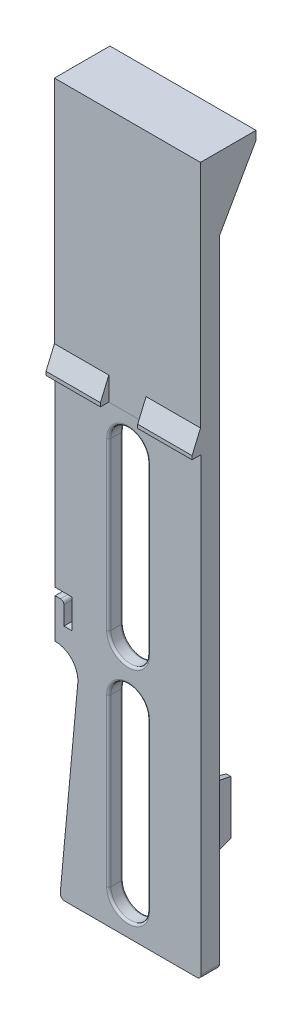
SolidWorks part; units mm, degrees
ref_plane "Front Plane" through (0, 0, 0) normal (0, 0, 1) x (1, 0, 0)
ref_plane "Top Plane" through (0, 0, 0) normal (0, 1, 0) x (1, 0, 0)
ref_plane "Right Plane" through (0, 0, 0) normal (1, 0, 0) x (0, 0, -1)
sketch "Sketch1" plane through (0, 0, 0) normal (0, 0, 1) x (1, 0, 0)
  line L0 (0, 0) -> (0, 100.3393) construction
  line L2 (-12.7, 123.19) -> (12.7, 123.19)
  line L3 (-12.7, 123.19) -> (-12.7, 0)
  line L4 (-12.7, 0) -> (12.7, 0)
  line L5 (12.7, 123.19) -> (12.7, 0)
  line L6 (-12.7, 123.19) -> (12.7, 0) construction
  line L7 (-12.7, 0) -> (12.7, 123.19) construction
  point P3 (0, 61.595)
  dimension "D1" = 25.4
  dimension "D2" = 123.19
extrude "Boss-Extrude1" add sketch "Sketch1" against normal blind 2.032
sketch "Sketch2" plane through (0, 0, -2.032) normal (0, 0, -1) x (-1, 0, 0)
  line L4 (-12.7, 123.19) -> (-12.7, 0)
  line L5 (-12.7, 0) -> (12.7, 0)
  line L6 (12.7, 0) -> (12.7, 123.19)
  line L7 (12.7, 123.19) -> (-12.7, 123.19)
  line L8 (-12.7, 123.19) -> (-12.7, 0)
  line L9 (-12.7, 0) -> (12.7, 0)
  line L10 (12.7, 0) -> (12.7, 123.19)
  line L11 (12.7, 123.19) -> (-12.7, 123.19)
  dimension "D1" = 0
extrude "Extrude-Thin1" add sketch "Sketch2" along normal offset from surface (1.143 mm away) 3.175 thin up to face at (0, 61.595, 0) thin type one direction reverse wall 1.524
sketch "Sketch3" plane through (0, 0, 0) normal (0, 0, 1) x (1, 0, 0)
  line L0 (0, 123.19) -> (0, 0) construction
  line L1 (12.7, 123.19) -> (-12.7, 123.19) construction
  line L2 (0, 34.7345) -> (0, 5.8293) construction
  line L3 (3.3655, 34.7345) -> (3.3655, 5.8293)
  line L4 (-3.3655, 34.7345) -> (-3.3655, 5.8293)
  line L5 (-12.7, 0) -> (12.7, 0) construction
  arc A0 (3.3655, 34.7345) -> (-3.3655, 34.7345) centre (0, 34.7345) ccw
  arc A1 (-3.3655, 5.8293) -> (3.3655, 5.8293) centre (0, 5.8293) ccw
  point P7 (0, 20.2819)
  dimension "D3" = 2.4638
  dimension "D1" = 6.731
  dimension "D2" = 35.6362
extrude "Cut-Extrude1" cut sketch "Sketch3" against normal through all
pattern_linear "LPattern1" count 2 spacing 38.608 along (0, 1, 0) of "Cut-Extrude1"
sketch "Sketch4" plane through (0, 0, 0) normal (0, 0, 1) x (1, 0, 0)
  line L0 (-11.8872, 0) -> (-8.763, 33.9877)
  line L1 (-12.7, 0) -> (12.7, 0) construction
  line L2 (-12.7, 38.3032) -> (-22.3348, 38.3032) construction
  line L3 (-12.7, 123.19) -> (-12.7, 0) construction
  line L4 (12.7, 0) -> (12.7, 123.19) construction
  arc A0 (-8.763, 33.9877) -> (-12.7, 38.3032) centre (-12.7, 34.3496) ccw
  dimension "D1" = 24.5872
  dimension "D2" = 38.3032
  dimension "D3" = 21.463
extrude "Cut-Extrude2" cut sketch "Sketch4" against normal through all and the other way through all
sketch "Sketch5" plane through (0, 0, 0) normal (0, 0, 1) x (1, 0, 0)
  line L0 (-12.7, 46.4312) -> (-9.7282, 46.4312)
  line L1 (-12.7, 123.19) -> (-12.7, 38.3032) construction
  line L2 (-9.7282, 46.4312) -> (-9.7282, 41.3512)
  line L3 (-9.7282, 41.3512) -> (-11.176, 41.3512)
  line L4 (-11.176, 41.3512) -> (-11.176, 45.1612)
  line L5 (-11.176, 45.1612) -> (-12.7, 45.1612)
  line L6 (-12.7, 45.1612) -> (-12.7, 46.4312)
  line L7 (-11.8872, 0) -> (12.7, 0) construction
  dimension "D1" = 1.27
  dimension "D2" = 1.4478
  dimension "D3" = 5.08
  dimension "D4" = 1.524
  dimension "D5" = 45.1612
extrude "Cut-Extrude3" cut sketch "Sketch5" against normal through all
sketch "Sketch6" plane through (0, 0, -2.032) normal (0, 0, -1) x (-1, 0, 0)
  line L0 (0, 0) -> (0, 133.807) construction
  line L1 (0, 6.0808) -> (0, 72.6186) construction
  line L2 (-7.1374, 6.0808) -> (-7.1374, 72.6186)
  line L3 (7.1374, 6.0808) -> (7.1374, 72.6186)
  line L4 (11.8872, 0) -> (-12.7, 0) construction
  line L5 (-8.7884, 6.0808) -> (-8.7884, 72.6186)
  line L6 (8.7884, 6.0808) -> (8.7884, 72.6186)
  arc A0 (-7.1374, 6.0808) -> (7.1374, 6.0808) centre (0, 6.0808) ccw
  arc A1 (7.1374, 72.6186) -> (-7.1374, 72.6186) centre (0, 72.6186) ccw
  arc A2 (8.7884, 72.6186) -> (-8.7884, 72.6186) centre (0, 72.6186) ccw
  arc A3 (-8.7884, 6.0808) -> (8.7884, 6.0808) centre (0, 6.0808) ccw
  point P5 (0, 39.3497)
  dimension "D3" = 79.756
  dimension "D1" = 14.2748
  dimension "D2" = 80.8126
  dimension "D4" = 1.651
extrude "Boss-Extrude2" add sketch "Sketch6" along normal up to surface (1.143 mm away) up to face at (-3.1127, 53.9418, -3.175)
sketch "Sketch7" plane through (0, 0, -3.175) normal (0, 0, -1) x (-1, 0, 0)
  line L1 (-6.3451, 0) -> (7.3026, 0)
  line L2 (-6.3451, 0) -> (-6.3451, -4.1989)
  line L3 (-6.3451, -4.1989) -> (7.3026, -4.1989)
  line L4 (7.3026, 0) -> (7.3026, -4.1989)
extrude "Cut-Extrude4" cut sketch "Sketch7" against normal through all
sketch "Sketch8" plane through (0, 0, -3.175) normal (0, 0, -1) x (-1, 0, 0)
  circle A0 centre (0, 6.0808) radius 7.1374
extrude "Cut-Extrude5" cut sketch "Sketch8" against normal up to surface (1.143 mm away) up to face at (0, 27.8828, -2.032)
fillet "Fillet1" radius 0.254 2 edges at (-3.7372, 0, -2.6035) (3.7372, 0, -2.6035)
sketch "Sketch9" plane through (0, 0, -2.032) normal (0, 0, -1) x (-1, 0, 0)
  line L0 (3.3655, 34.7345) -> (3.3655, 5.8293) construction
  line L1 (-3.3655, 5.8293) -> (-3.3655, 34.7345) construction
  line L2 (-3.3655, 44.4373) -> (-3.3655, 73.3425) construction
  line L3 (-7.1374, 72.6186) -> (-7.1374, 6.0808)
  line L4 (-4.5477, 0) -> (4.5477, 0)
  line L5 (7.1374, 6.0808) -> (7.1374, 72.6186)
  line L6 (-7.1374, 72.6186) -> (-7.1374, 6.0808)
  line L7 (-4.5477, 0) -> (4.5477, 0)
  line L8 (7.1374, 6.0808) -> (7.1374, 72.6186)
  line L9 (3.3655, 73.3425) -> (3.3655, 44.4373) construction
  line L10 (3.3655, 34.7345) -> (3.3655, 5.8293)
  line L11 (-3.3655, 5.8293) -> (-3.3655, 34.7345)
  line L12 (-3.3655, 44.4373) -> (-3.3655, 73.3425)
  line L13 (3.3655, 73.3425) -> (3.3655, 44.4373)
  arc A0 (-3.3655, 5.8293) -> (3.3655, 5.8293) centre (0, 5.8293) ccw construction
  arc A1 (-3.3655, 5.8293) -> (3.3655, 5.8293) centre (0, 5.8293) ccw
  arc A2 (3.3655, 34.7345) -> (-3.3655, 34.7345) centre (0, 34.7345) ccw construction
  arc A3 (-3.3655, 44.4373) -> (3.3655, 44.4373) centre (0, 44.4373) ccw construction
  arc A4 (3.3655, 34.7345) -> (-3.3655, 34.7345) centre (0, 34.7345) ccw
  arc A5 (-7.1374, 6.0808) -> (-4.3914, 0.4542) centre (0, 6.0808) ccw
  arc A6 (-4.5477, 0) -> (-4.3914, 0.4542) centre (-4.5477, 0.254) ccw
  arc A7 (4.3914, 0.4542) -> (4.5477, 0) centre (4.5477, 0.254) ccw
  arc A8 (4.3914, 0.4542) -> (7.1374, 6.0808) centre (0, 6.0808) ccw
  arc A9 (7.1374, 72.6186) -> (-7.1374, 72.6186) centre (0, 72.6186) ccw
  arc A10 (-7.1374, 6.0808) -> (-4.3914, 0.4542) centre (0, 6.0808) ccw
  arc A11 (-4.5477, 0) -> (-4.3914, 0.4542) centre (-4.5477, 0.254) ccw
  arc A12 (4.3914, 0.4542) -> (4.5477, 0) centre (4.5477, 0.254) ccw
  arc A13 (4.3914, 0.4542) -> (7.1374, 6.0808) centre (0, 6.0808) ccw
  arc A14 (7.1374, 72.6186) -> (-7.1374, 72.6186) centre (0, 72.6186) ccw
  arc A15 (-3.3655, 44.4373) -> (3.3655, 44.4373) centre (0, 44.4373) ccw
  arc A16 (3.3655, 73.3425) -> (-3.3655, 73.3425) centre (0, 73.3425) ccw construction
  arc A17 (3.3655, 73.3425) -> (-3.3655, 73.3425) centre (0, 73.3425) ccw
  dimension "D1" = 0
extrude "Boss-Extrude3" add sketch "Sketch9" along normal blind 0.508
sketch "Sketch10" plane through (0, 0, -2.032) normal (0, 0, -1) x (-1, 0, 0)
  line L0 (8.7884, 34.9243) -> (8.7884, 72.6186) construction
  line L1 (11.176, 37.9977) -> (11.176, 41.3512) construction
  line L2 (11.176, 41.3512) -> (9.7282, 41.3512) construction
  line L3 (9.7282, 41.3512) -> (9.7282, 46.4312) construction
  line L4 (9.7282, 46.4312) -> (11.176, 46.4312) construction
  line L5 (8.7884, 34.9243) -> (8.7884, 48.0822)
  line L6 (11.176, 37.9977) -> (11.176, 41.3512)
  line L7 (11.176, 41.3512) -> (9.7282, 41.3512)
  line L8 (9.7282, 41.3512) -> (9.7282, 46.4312)
  line L9 (9.7282, 46.4312) -> (11.176, 46.4312)
  line L10 (11.176, 46.4312) -> (11.176, 121.666) construction
  line L11 (11.176, 46.4312) -> (11.176, 48.0822)
  line L12 (11.176, 48.0822) -> (8.7884, 48.0822)
  arc A0 (11.176, 37.9977) -> (8.7884, 34.9243) centre (12.7, 34.3496) ccw construction
  arc A1 (11.176, 37.9977) -> (8.7884, 34.9243) centre (12.7, 34.3496) ccw
  dimension "D1" = 1.651
extrude "Boss-Extrude4" add sketch "Sketch10" along normal up to surface (1.143 mm away) up to face at (-11.9342, 41.6747, -3.175)
sketch "Sketch11" plane through (0, 0, -2.032) normal (0, 0, -1) x (-1, 0, 0)
  line L0 (8.7884, 72.6186) -> (8.7884, 121.666)
  line L1 (-8.7884, 72.6186) -> (-8.7884, 121.666)
  line L2 (11.176, 121.666) -> (-11.176, 121.666) construction
  line L3 (8.7884, 121.666) -> (7.1374, 121.666)
  line L4 (0, 0) -> (0, 145.7514) construction
  line L5 (-7.1374, 72.6186) -> (-7.1374, 121.666)
  line L7 (7.1374, 72.6186) -> (7.1374, 121.666)
  line L8 (-8.7884, 72.6186) -> (-7.1374, 72.6186)
  line L9 (7.1374, 72.6186) -> (8.7884, 72.6186)
  line L10 (-7.1374, 121.666) -> (-8.7884, 121.666)
  dimension "D1" = 1.651
  dimension "D2" = 1.651
extrude "Boss-Extrude5" add sketch "Sketch11" along normal up to surface (1.143 mm away)
sketch "Sketch12" plane through (0, 0, -2.032) normal (0, 0, -1) x (-1, 0, 0)
  line L0 (0, 0) -> (0, 135.5833) construction
  line L1 (0, 121.666) -> (0, 80.5241)
  line L2 (7.1374, 121.666) -> (-7.1374, 121.666) construction
  arc A1 (7.1374, 77.7463) -> (-7.1374, 77.7463) centre (0, 72.6186) ccw construction
  dimension "D1" = 7.9055
extrude "Extrude-Thin4" add sketch "Sketch12" along normal up to surface (1.143 mm away) thin thin type mid plane wall 1.651
sketch "Sketch13" plane through (0, 0, -2.032) normal (0, 0, -1) x (-1, 0, 0)
  line L0 (9.9822, 48.0822) -> (9.9822, 56.894) construction
  line L1 (11.176, 48.0822) -> (8.7884, 48.0822) construction
  line L2 (9.9822, 50.8308) -> (-19.4969, 49.4381) construction
  circle A0 centre (9.9822, 50.8308) radius 1.3927
  circle A1 centre (-10.0834, 49.8828) radius 1.4426
extrude "Boss-Extrude6" add sketch "Sketch13" along normal up to surface (1.143 mm away)
sketch "Sketch14" plane through (0, 0, -2.032) normal (0, 0, -1) x (-1, 0, 0)
  line L4 (7.5148, 1.524) -> (11.176, 1.524)
  line L5 (11.176, 1.524) -> (11.176, 7.737)
  line L6 (11.176, 7.737) -> (8.7884, 33.7114)
  line L7 (8.7884, 33.7114) -> (8.7884, 6.0808)
  line L8 (7.5148, 1.524) -> (11.176, 1.524)
  line L9 (11.176, 1.524) -> (11.176, 7.737)
  line L10 (11.176, 7.737) -> (8.7884, 33.7114)
  line L11 (8.7884, 33.7114) -> (8.7884, 6.0808)
  arc A1 (7.5148, 1.524) -> (8.7884, 6.0808) centre (0, 6.0808) ccw
  arc A2 (7.5148, 1.524) -> (8.7884, 6.0808) centre (0, 6.0808) ccw
  dimension "D1" = 0
extrude "Boss-Extrude7" add sketch "Sketch14" along normal up to surface (1.143 mm away)
fillet "Fillet2" radius 0.381 16 edges at (0, 76.708, 0) (3.3655, 58.8899, 0) (0, 41.0718, 0) (0, 38.1, 0) (3.3655, 20.2819, 0) (0, 2.4638, 0) (0, 38.1, -2.54) (-3.3655, 20.2819, -2.54) (0, 2.4638, -2.54) (0, 76.708, -2.54) (-3.3655, 58.8899, -2.54) (0, 41.0718, -2.54) (-3.3655, 58.8899, 0) (-3.3655, 20.2819, 0) (3.3655, 20.2819, -2.54) (3.3655, 58.8899, -2.54)
sketch "Sketch15" plane through (0, 0, 0) normal (0, 0, 1) x (1, 0, 0)
  line L0 (-12.7, 123.19) -> (-12.7, 46.4312) construction
  line L1 (12.7, 123.19) -> (-12.7, 123.19) construction
  line L2 (12.7, 0) -> (12.7, 123.19) construction
  line L3 (-12.7, 123.19) -> (-12.7, 79.121)
  line L4 (12.7, 123.19) -> (-12.7, 123.19)
  line L5 (12.7, 79.121) -> (12.7, 123.19)
  line L6 (-12.7, 79.121) -> (12.7, 79.121)
  dimension "D1" = 44.069
extrude "Boss-Extrude8" add sketch "Sketch15" along normal blind 0.127
sketch "Sketch16" plane through (0, 0, 0) normal (1, 0, 0) x (0, 0, -1)
  line L0 (-0.127, 79.121) -> (-1.5875, 79.121)
  line L1 (-1.5875, 79.121) -> (-1.5875, 79.756)
  line L2 (-1.5875, 79.756) -> (-0.127, 83.185)
  line L3 (-0.127, 79.121) -> (-0.127, 123.19) construction
  line L4 (-0.127, 83.185) -> (-0.127, 79.121)
  line L5 (0, 0) -> (0, 79.121) construction
  dimension "D1" = 1.5875
  dimension "D2" = 0.635
  dimension "D3" = 4.064
extrude "Boss-Extrude9" add sketch "Sketch16" along normal up to surface and the other way up to surface up to face at (12.7, 67.437, -1.016) other way up to face at (-12.7, 41.7322, -1.5875)
sketch "Sketch17" plane through (0, 123.19, 0) normal (0, 1, 0) x (1, 0, 0)
  line L0 (0, -0.127) -> (0, -13.26) construction
  line L1 (12.7, -0.127) -> (-12.7, -0.127) construction
  line L3 (-3.2385, -6.3417) -> (3.2385, -6.3417)
  line L4 (-3.2385, -6.3417) -> (-3.2385, -0.127)
  line L5 (-3.2385, -0.127) -> (3.2385, -0.127)
  line L6 (3.2385, -6.3417) -> (3.2385, -0.127)
  line L7 (-3.2385, -6.3417) -> (3.2385, -0.127) construction
  line L8 (-3.2385, -0.127) -> (3.2385, -6.3417) construction
  point P5 (0, -3.2343)
  dimension "D1" = 6.477
extrude "Cut-Extrude6" cut sketch "Sketch17" against normal through all
fillet "Fillet3" radius 0.5842 1 edges at (-11.176, 45.1612, -1.5875)
sketch "Sketch18" plane through (0, 0, -3.175) normal (0, 0, -1) x (-1, 0, 0)
  line L0 (-7.1374, 6.0808) -> (-7.1374, 72.6186) construction
  line L1 (-7.1374, 25.4) -> (-8.7884, 25.4)
  line L2 (-7.1374, 25.4) -> (-7.1374, 12.7)
  line L3 (-7.1374, 12.7) -> (-8.7884, 12.7)
  line L4 (-8.7884, 25.4) -> (-8.7884, 12.7)
  line L5 (-8.7884, 6.0808) -> (-8.7884, 49.2472) construction
  line L6 (-4.5477, 0) -> (-12.7, 0) construction
  dimension "D1" = 12.7
  dimension "D2" = 12.7
extrude "Boss-Extrude11" add sketch "Sketch18" along normal blind 6.35 draft 4
sketch "Sketch19" plane through (12.7, 0, 0) normal (1, 0, 0) x (0, 0, -1)
  line L0 (3.175, 12.7) -> (12.9126, 12.7)
  line L1 (3.175, 12.7) -> (11.2695, 14.8689)
  line L2 (11.2695, 14.8689) -> (12.9126, 12.7)
  line L3 (3.175, 25.4) -> (14.8026, 25.4)
  line L4 (3.175, 25.4) -> (12.7147, 22.8438)
  line L5 (12.7147, 22.8438) -> (14.8026, 25.4)
  dimension "D1" = 15
  dimension "D2" = 15
extrude "Cut-Extrude7" cut sketch "Sketch19" against normal through all
fillet "Fillet4" radius 0.762 2 edges at (-11.8872, 0, -1.5875) (12.7, 0, -1.5875)
sketch "Sketch20" plane through (0, 0, 0) normal (0, 0, 1) x (1, 0, 0)
  line L0 (-8.763, 33.9877) -> (-11.8107, 0.8318) construction
  line L1 (-8.763, 33.9877) -> (-11.8107, 0.8318)
  arc A0 (-8.763, 33.9877) -> (-12.7, 38.3032) centre (-12.7, 34.3496) ccw construction
  arc A1 (-8.763, 33.9877) -> (-12.7, 38.3032) centre (-12.7, 34.3496) ccw
extrude "Cut-Extrude8" cut sketch "Sketch20" against normal through all and the other way through all flip side to cut
sketch "Sketch22" plane through (0, 0, -3.175) normal (0, 0, -1) x (-1, 0, 0)
  line L0 (-12.7, 123.19) -> (12.7, 123.19) construction
  line L1 (-12.7, 123.19) -> (12.7, 123.19)
  line L3 (-11.176, 121.666) -> (-8.7884, 121.666) construction
  line L6 (-7.1374, 121.666) -> (-0.8255, 121.666) construction
  line L7 (0.8255, 121.666) -> (7.1374, 121.666) construction
  line L8 (8.7884, 121.666) -> (11.176, 121.666) construction
  line L9 (-11.176, 121.666) -> (-8.7884, 121.666)
  line L10 (-7.1374, 121.666) -> (-0.8255, 121.666)
  line L11 (0.8255, 121.666) -> (7.1374, 121.666)
  line L12 (8.7884, 121.666) -> (11.176, 121.666)
  line L13 (-12.7, 0.762) -> (-12.7, 123.19) construction
  line L14 (-11.176, 50.8247) -> (-11.176, 121.666) construction
  line L15 (-8.7884, 50.5184) -> (-8.7884, 121.666) construction
  line L16 (-7.1374, 121.666) -> (-7.1374, 77.7463) construction
  line L17 (-0.8255, 81.3681) -> (-0.8255, 121.666) construction
  line L18 (0.8255, 81.3681) -> (0.8255, 121.666) construction
  line L19 (7.1374, 77.7463) -> (7.1374, 121.666) construction
  line L20 (8.7884, 121.666) -> (8.7884, 51.5479) construction
  line L21 (11.176, 121.666) -> (11.176, 51.5479) construction
  line L22 (12.7, 123.19) -> (12.7, 46.4312) construction
  line L23 (-12.7, 110.49) -> (-12.7, 123.19)
  line L24 (-11.176, 110.49) -> (-11.176, 121.666)
  line L25 (-8.7884, 110.49) -> (-8.7884, 121.666)
  line L26 (-7.1374, 121.666) -> (-7.1374, 110.49)
  line L27 (-0.8255, 110.49) -> (-0.8255, 121.666)
  line L28 (0.8255, 110.49) -> (0.8255, 121.666)
  line L29 (7.1374, 110.49) -> (7.1374, 121.666)
  line L30 (8.7884, 121.666) -> (8.7884, 110.49)
  line L31 (11.176, 121.666) -> (11.176, 110.49)
  line L32 (12.7, 123.19) -> (12.7, 110.49)
  line L33 (-12.7, 110.49) -> (-11.176, 110.49)
  line L34 (-8.7884, 110.49) -> (-7.1374, 110.49)
  line L35 (11.176, 110.49) -> (12.7, 110.49)
  line L36 (7.1374, 110.49) -> (8.7884, 110.49)
  line L37 (-0.8255, 110.49) -> (0.8255, 110.49)
  dimension "D1" = 12.7
extrude "Boss-Extrude12" add sketch "Sketch22" along normal blind 6.35
sketch "Sketch23" plane through (-12.7, 0, 0) normal (-1, 0, 0) x (0, 0, 1)
  line L0 (-3.175, 110.49) -> (-9.525, 121.666)
  line L2 (-9.525, 121.666) -> (-9.525, 110.49) construction
  line L3 (-9.525, 121.666) -> (-9.525, 110.49)
  line L4 (-9.525, 110.49) -> (-3.175, 110.49) construction
  line L5 (-9.525, 110.49) -> (-3.175, 110.49)
extrude "Cut-Extrude9" cut sketch "Sketch23" against normal through all
